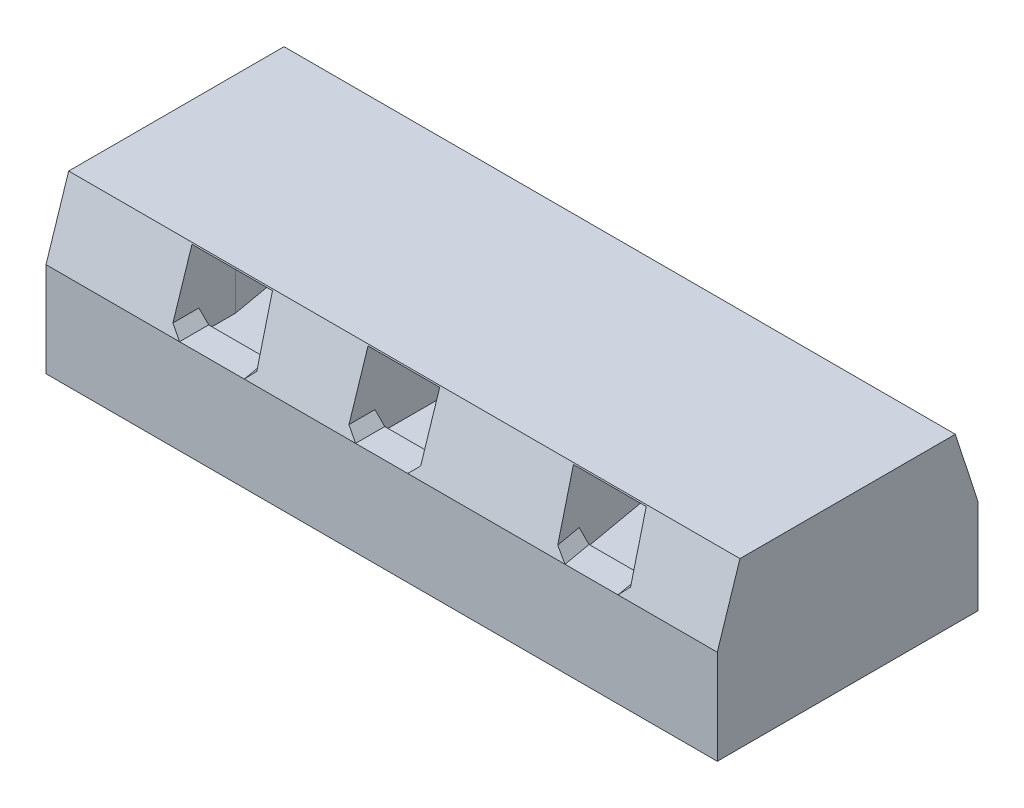
SolidWorks part; units mm, degrees
ref_plane "前视基准面" through (0, 0, 0) normal (0, 0, 1) x (1, 0, 0)
ref_plane "上视基准面" through (0, 0, 0) normal (0, 1, 0) x (1, 0, 0)
ref_plane "右视基准面" through (0, 0, 0) normal (1, 0, 0) x (0, 0, -1)
other "Configuration Table"
sketch "草图1" plane through (0, 0, 0) normal (0, 1, 0) x (1, 0, 0)
  line L1 (-1030, -400) -> (1030, -400)
  line L2 (-1030, -400) -> (-1030, 400)
  line L3 (-1030, 400) -> (1030, 400)
  line L4 (1030, -400) -> (1030, 400)
  line L5 (-1030, -400) -> (1030, 400) construction
  line L6 (-1030, 400) -> (1030, -400) construction
  point P0 (0, 0)
  dimension "D1" = 2060
  dimension "D2" = 800
extrude "凸台-拉伸1" add sketch "草图1" along normal blind 500
sketch "草图3" plane through (0, 0, 0) normal (0, 0, 1) x (1, 0, 0)
  line L0 (0, 0) -> (0, 50000) construction
  line L1 (-1030, 0) -> (1030, 0) construction
  line L2 (-110, 250) -> (110, 250)
  line L3 (-110, 250) -> (-110, 470)
  line L4 (-110, 470) -> (110, 470)
  line L5 (110, 250) -> (110, 470)
  line L6 (-110, 250) -> (110, 470) construction
  line L7 (-110, 470) -> (110, 250) construction
  point P3 (0, 360)
  dimension "D1" = 220
  dimension "D2" = 220
  dimension "D3" = 250
extrude "切除-拉伸1" cut sketch "草图3" against normal mid plane 621
sketch "草图22" plane through (1030, 0, 0) normal (1, 0, 0) x (0, 0, -1)
  line L0 (0, 0) -> (0, 50000) construction
  line L1 (-330.4672, 504) -> (-400, 290)
  line L3 (-400, 500) -> (-400, 0) construction
  line L4 (-400, 500) -> (400, 500) construction
  line L5 (-330.4672, 504) -> (330.4672, 504)
  line L6 (330.4672, 504) -> (400, 290)
  line L7 (-400, 290) -> (400, 290)
  line L8 (-400, 290) -> (-400, 0)
  line L9 (-400, 0) -> (400, 0)
  line L10 (400, 0) -> (400, 290)
  point P9 (0, 504)
  line M8 (400, 500) -> (-400, 500)
  dimension "D1" = 290
  dimension "D2" = 18
  dimension "D3" = 4
extrude "凸台-拉伸2" add sketch "草图22" against normal up to surface (2060 mm away) contours L7 L0 L1 M8 | L0 L7 L6 M8 up to face at (-1030, 250, 0)
sketch "草图5" plane through (0, 0, 400) normal (0, 0, 1) x (1, 0, 0)
  line L1 (-110, 290) -> (110, 290)
  line L2 (-110, 290) -> (-110, 500)
  line L3 (-110, 500) -> (110, 500)
  line L4 (110, 290) -> (110, 500)
  line L5 (-110, 290) -> (110, 500) construction
  line L6 (-110, 500) -> (110, 290) construction
  line L7 (-1030, 0) -> (1030, 0) construction
  point P0 (0, 395)
  dimension "D1" = 220
  dimension "D2" = 290
  dimension "D3" = 210
extrude "切除-拉伸2" cut sketch "草图5" against normal through all
sketch "草图6" plane through (0, 500, 0) normal (0, 1, 0) x (1, 0, 0)
  line L0 (-619.2844, 259.8308) -> (8063.1245, -48980.5568) construction
  line L1 (0, 0) -> (0, 50000) construction
  line L2 (-110, 400) -> (-1030, 400) construction
  line L3 (-110, 400) -> (-1030, 400)
  point P7 (-644, 400)
  dimension "D1" = 10
  dimension "D2" = 644
ref_plane "基准面1" through (37.3457, 0, 211.7982) normal (0.1736, 0, 0.9848) x (0.9848, 0, -0.1736)
sketch "草图7" plane through (37.3457, 0, 211.7982) normal (0.1736, 0, 0.9848) x (0.9848, 0, -0.1736)
  line L0 (-38.8696, 500) -> (-944.8927, 500) construction
  line L1 (-674.7569, 290) -> (-454.7569, 290)
  line L2 (-674.7569, 290) -> (-674.7569, 500)
  line L3 (-674.7569, 500) -> (-454.7569, 500)
  line L4 (-454.7569, 290) -> (-454.7569, 500)
  line L5 (-674.7569, 290) -> (-454.7569, 500) construction
  line L6 (-674.7569, 500) -> (-454.7569, 290) construction
  line L7 (-1083.8113, 0) -> (944.8927, 0) construction
  line L8 (-564.7569, 395) -> (-564.7569, 500)
  point P0 (-564.7569, 395)
  dimension "D1" = 220
  dimension "D2" = 290
extrude "切除-拉伸3" cut sketch "草图7" against normal through all both and the other way through all
sketch "草图10" plane through (0, 290, 0) normal (0, 1, 0) x (1, 0, 0)
  line L2 (-532.3031, 400) -> (-520.2717, 331.7669) construction
  line L3 (-391.2415, -310.5) -> (-614.6353, -310.5)
  line L4 (-407.0228, -310.5) -> (-630.4166, -310.5)
  line L5 (-755.6969, 400) -> (-743.6656, 331.7669) construction
  line L6 (-532.3031, 400) -> (-520.2717, 331.7669)
  line L7 (-755.6969, 400) -> (-743.6656, 331.7669)
  line L8 (0, 0) -> (50000, 0) construction
  line L9 (-739.9157, 310.5) -> (-516.5218, 310.5)
  line L10 (-110, 400) -> (-1030, 400) construction
  line M1 (-755.6969, 400) -> (-614.6353, -400)
  line M3 (-391.2415, -400) -> (-532.3031, 400)
  dimension "D2" = 89.5
  dimension "D1" = 89.5
extrude "切除-拉伸4" cut sketch "草图10" against normal blind 40 contours L7 L8 L6 L9 | L8 L4 M1 M3
sketch "草图13" plane through (0, 500, 0) normal (0, 1, 0) x (1, 0, 0)
  line L0 (501.2252, 409.7163) -> (-8181.1837, 49650.104) construction
  line L2 (-35348.9199, 197221.3814) -> (42792.76, -245942.1074) construction
  line L3 (110, -400) -> (1030, -400) construction
  line L4 (0, -200000) -> (0, 250000) construction
  point P4 (644, -400)
  dimension "D1" = 644
sketch "草图14" plane through (37.3457, 0, 211.7982) normal (0.1736, 0, 0.9848) x (0.9848, 0, -0.1736)
  line L0 (-34729.6355, 500) -> (43412.0444, 500) construction
  line L1 (454.7569, 290) -> (674.7569, 290)
  line L2 (454.7569, 290) -> (454.7569, 500)
  line L3 (454.7569, 500) -> (674.7569, 500)
  line L4 (674.7569, 290) -> (674.7569, 500)
  line L5 (454.7569, 290) -> (674.7569, 500) construction
  line L6 (454.7569, 500) -> (674.7569, 290) construction
  line L7 (564.7569, 395) -> (564.7569, 500)
  line L8 (-1083.8113, 0) -> (944.8927, 0) construction
  point P0 (564.7569, 395)
  dimension "D1" = 220
  dimension "D2" = 290
extrude "切除-拉伸5" cut sketch "草图14" against normal through all both and the other way through all
sketch "草图15" plane through (0, 290, 0) normal (0, 1, 0) x (1, 0, 0)
  line L0 (110, 310.5) -> (1030, 310.5)
  line L1 (1030, -400) -> (1030, -331.7669) construction
  line L2 (110, -310.5) -> (1030, -310.5)
  line L3 (614.6353, 400) -> (755.6969, -400) construction
  line L4 (391.2415, 400) -> (532.3031, -400) construction
  line L5 (614.6353, 400) -> (755.6969, -400)
  line L6 (391.2415, 400) -> (532.3031, -400)
  line M1 (391.2415, 400) -> (532.3031, -400)
  line M3 (755.6969, -400) -> (614.6353, 400)
extrude "切除-拉伸6" cut sketch "草图15" against normal blind 40 contours L2 L0 M1 M3
sketch "草图16" plane through (0, 0, -400) normal (0, 0, -1) x (-1, 0, 0)
  line L0 (35348.9199, 500) -> (-42792.76, 500) construction
  line L1 (-650.2415, 500) -> (-614.6353, 500)
  line L2 (-650.2415, 500) -> (-650.2415, 290)
  line L3 (-650.2415, 290) -> (-614.6353, 290)
  line L4 (-614.6353, 500) -> (-614.6353, 290)
  line L5 (-391.2415, 290) -> (-391.2415, 500) construction
  dimension "D1" = 259
extrude "切除-拉伸7" cut sketch "草图16" against normal through all both and the other way through all
sketch "草图18" plane through (0, 0, 400) normal (0, 0, 1) x (1, 0, 0)
  line L0 (-110, 500) -> (-1030, 500) construction
  line L1 (-650.2415, 500) -> (-614.6353, 500)
  line L2 (-650.2415, 500) -> (-650.2415, 290)
  line L3 (-650.2415, 290) -> (-614.6353, 290)
  line L4 (-614.6353, 500) -> (-614.6353, 290)
  line L5 (-391.2415, 500) -> (-391.2415, 290) construction
  dimension "D1" = 259
extrude "切除-拉伸11" cut sketch "草图18" against normal through all
sketch "草图19" plane through (0, 290, 0) normal (0, 1, 0) x (1, 0, 0)
  line L0 (-630.4166, -310.5) -> (-650.2415, -310.5)
  line L5 (-407.0228, -310.5) -> (-630.4166, -310.5)
  line L6 (-630.4166, -310.5) -> (-650.2415, -198.0675)
  line L7 (-650.2415, -198.0675) -> (-650.2415, -400)
  line L8 (-650.2415, -400) -> (-391.2415, -400)
  line L9 (-391.2415, -400) -> (-407.0228, -310.5)
  line L10 (-407.0228, -310.5) -> (-630.4166, -310.5)
  line L11 (-630.4166, -310.5) -> (-650.2415, -198.0675)
  line L12 (-650.2415, -198.0675) -> (-650.2415, -400)
  line L13 (-650.2415, -400) -> (-391.2415, -400)
  line L14 (-391.2415, -400) -> (-407.0228, -310.5)
  line M7 (-630.4166, -310.5) -> (-650.2415, -198.0675)
  line M8 (-650.2415, -198.0675) -> (-650.2415, -400)
  dimension "D1" = 0
extrude "切除-拉伸12" cut sketch "草图19" against normal up to surface (40 mm away) contours L0 M7 M8 up to face at (-573.4692, 250, 0)
sketch "草图23" plane through (1030, 0, 0) normal (1, 0, 0) x (0, 0, -1)
  line L0 (400, 500) -> (400, 0) construction
  line L1 (330.4672, 504) -> (400, 290) construction
  line L2 (197221.3814, 500) -> (-245942.1074, 500) construction
  line L3 (-400, 500) -> (-400, 0) construction
  line L4 (-330.4672, 504) -> (-400, 290) construction
  line L5 (400, 500) -> (400, 290)
  line L6 (331.7669, 500) -> (400, 290)
  line L7 (400, 500) -> (331.7669, 500)
  line L8 (-400, 500) -> (-400, 290)
  line L9 (-331.7669, 500) -> (-400, 290)
  line L10 (-331.7669, 500) -> (-400, 500)
extrude "切除-拉伸15" cut sketch "草图23" against normal through all
chamfer "倒角1" distance 30 angle 45 6 edges at (747.8063, 290, 355.25) (524.4124, 290, 355.25) (110, 290, 355.25) (-110, 290, 355.25) (-399.1321, 290, 355.25) (-650.2415, 290, 355.25)
sketch "草图24" plane through (0, 290, 0) normal (0, 1, 0) x (1, 0, 0)
  line L0 (630.4166, 310.5) -> (650.2415, 310.5)
  line L5 (407.0228, 310.5) -> (630.4166, 310.5)
  line L6 (630.4166, 310.5) -> (650.2415, 198.0675)
  line L7 (650.2415, 198.0675) -> (650.2415, 400)
  line L8 (650.2415, 400) -> (391.2415, 400)
  line L9 (391.2415, 400) -> (407.0228, 310.5)
  line L10 (407.0228, 310.5) -> (630.4166, 310.5)
  line L11 (630.4166, 310.5) -> (650.2415, 198.0675)
  line L12 (650.2415, 198.0675) -> (650.2415, 400)
  line L13 (650.2415, 400) -> (391.2415, 400)
  line L14 (391.2415, 400) -> (407.0228, 310.5)
  line M7 (630.4166, 310.5) -> (650.2415, 198.0675)
  line M8 (650.2415, 198.0675) -> (650.2415, 400)
  dimension "D1" = 0
extrude "切除-拉伸16" cut sketch "草图24" against normal up to surface (40 mm away) contours L0 M7 M8 up to face at (573.4692, 250, 0)
chamfer "倒角2" distance 30 angle 45 6 edges at (650.2415, 290, -355.25) (399.1321, 290, -355.25) (110, 290, -355.25) (-110, 290, -355.25) (-524.4124, 290, -355.25) (-747.8063, 290, -355.25)
